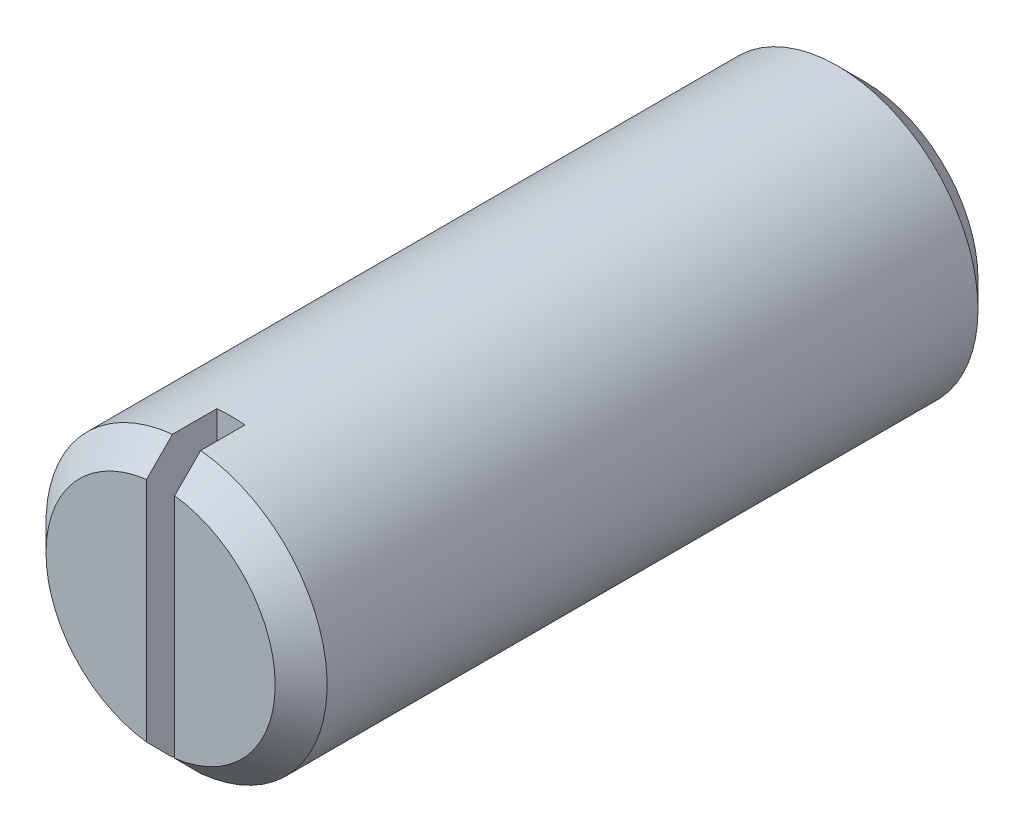
SolidWorks part; units mm, degrees
material "Сталь"
ref_plane "Спереди" through (0, 0, 0) normal (0, 0, 1) x (1, 0, 0)
ref_plane "Сверху" through (0, 0, 0) normal (0, 1, 0) x (1, 0, 0)
ref_plane "Справа" through (0, 0, 0) normal (1, 0, 0) x (0, 0, -1)
sketch "Эскиз1" plane through (0, 0, 0) normal (0, 0, 1) x (1, 0, 0)
  circle A0 centre (0, 0) radius 3
  dimension "D1" = 6
extrude "Бобышка-Вытянуть1" add sketch "Эскиз1" along normal blind 15
cosmetic thread "Условное изображение резьбы1" parameters "D2"=4.891
chamfer "Фаска1" distance 0.5545 angle 45 2 edges at (3, 0, 0) (3, 0, 15)
sketch "Эскиз2" plane through (0, 0, 15) normal (0, 0, 1) x (1, 0, 0)
  line L1 (-0.3, -3.5) -> (0.3, -3.5)
  line L2 (-0.3, -3.5) -> (-0.3, 3.5)
  line L3 (-0.3, 3.5) -> (0.3, 3.5)
  line L4 (0.3, -3.5) -> (0.3, 3.5)
  line L5 (-0.3, -3.5) -> (0.3, 3.5) construction
  line L6 (-0.3, 3.5) -> (0.3, -3.5) construction
  point P0 (0, 0)
  dimension "D1" = 0.6
  dimension "D2" = 7
extrude "Вырез-Вытянуть1" cut sketch "Эскиз2" against normal blind 1.5
